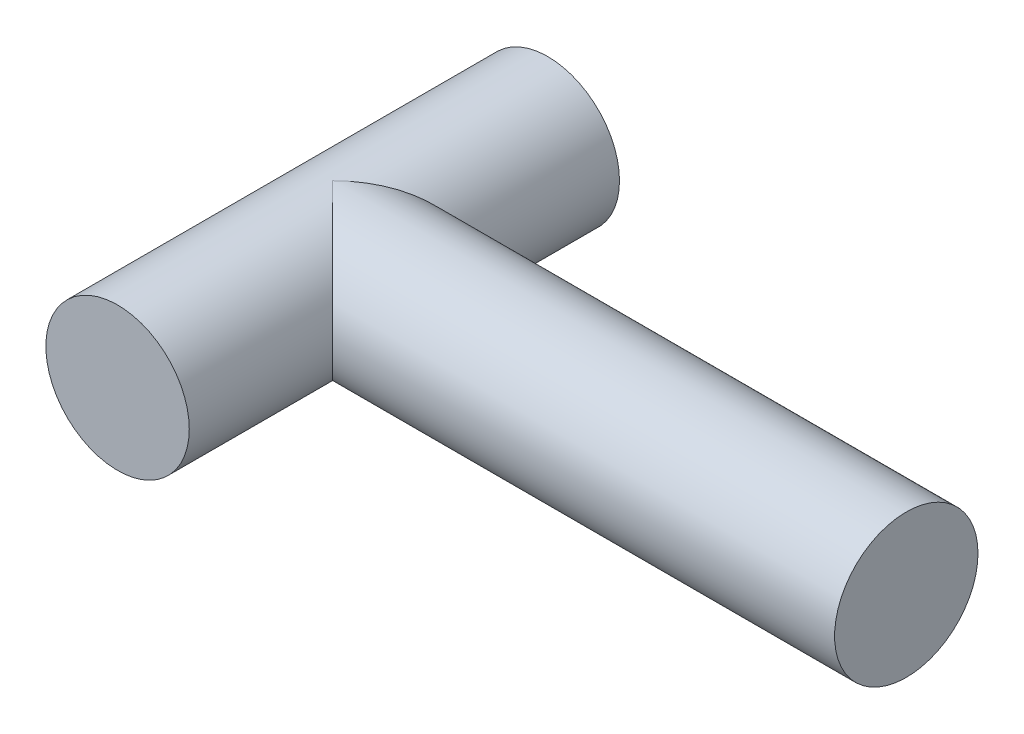
SolidWorks part; units mm, degrees
ref_plane "Front Plane" through (0, 0, 0) normal (0, 0, 1) x (1, 0, 0)
ref_plane "Top Plane" through (0, 0, 0) normal (0, 1, 0) x (1, 0, 0)
ref_plane "Right Plane" through (0, 0, 0) normal (1, 0, 0) x (0, 0, -1)
sketch "Sketch1" plane through (0, 0, 0) normal (0, 0, 1) x (1, 0, 0)
  circle A0 centre (0, 0) radius 7.5
  dimension "D1" = 15
extrude "Boss-Extrude1" add sketch "Sketch1" along normal mid plane 45
sketch "Sketch2" plane through (0, 0, 0) normal (1, 0, 0) x (0, 0, -1)
  circle A0 centre (0, 0) radius 7.5
  dimension "D1" = 15
extrude "Boss-Extrude2" add sketch "Sketch2" along normal blind 60
